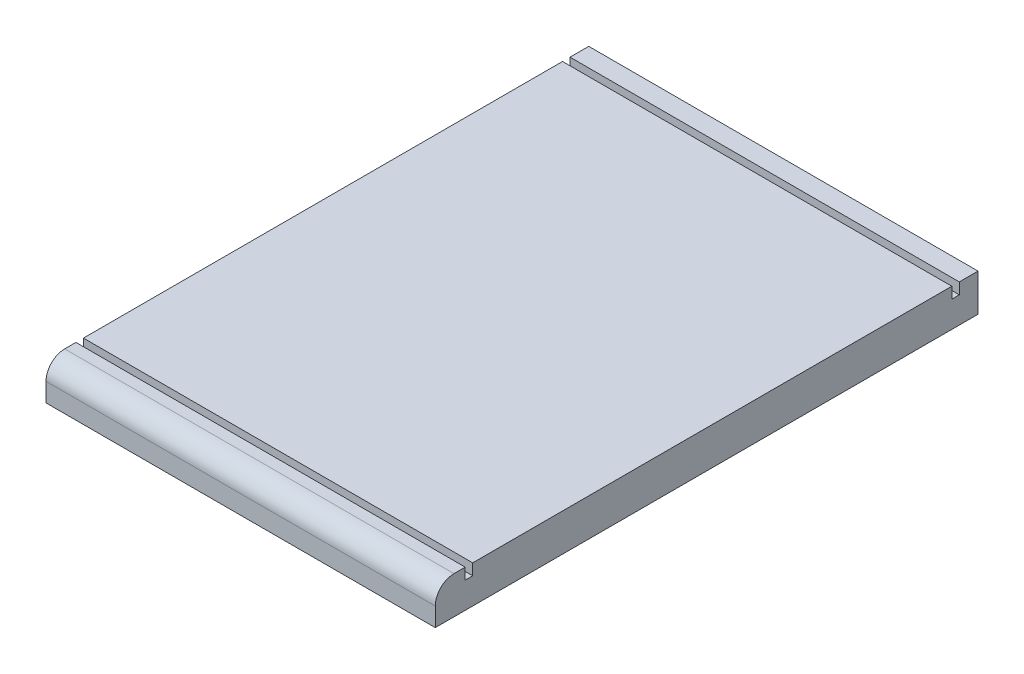
SolidWorks part; units mm, degrees
material "Mahogany"
ref_plane "Front Plane" through (0, 0, 0) normal (0, 0, 1) x (1, 0, 0)
ref_plane "Top Plane" through (0, 0, 0) normal (0, 1, 0) x (1, 0, 0)
ref_plane "Right Plane" through (0, 0, 0) normal (1, 0, 0) x (0, 0, -1)
sketch "Sketch1" plane through (0, 0, 0) normal (0, 1, 0) x (1, 0, 0)
  line L1 (-52, -72.5) -> (52, -72.5)
  line L2 (-52, -72.5) -> (-52, 72.5)
  line L3 (-52, 72.5) -> (52, 72.5)
  line L4 (52, -72.5) -> (52, 72.5)
  line L5 (-52, -72.5) -> (52, 72.5) construction
  line L6 (-52, 72.5) -> (52, -72.5) construction
  point P0 (0, 0)
  dimension "D1" = 104
  dimension "D2" = 145
extrude "Boss-Extrude1" add sketch "Sketch1" along normal blind 10
sketch "Sketch2" plane through (0, 10, 0) normal (0, 1, 0) x (1, 0, 0)
  line L0 (-52, 72.5) -> (-52, -72.5) construction
  line L1 (-52, 67.5) -> (52, 67.5)
  line L2 (-52, 67.5) -> (-52, 65.5)
  line L3 (-52, 65.5) -> (52, 65.5)
  line L4 (52, 67.5) -> (52, 65.5)
  line L5 (52, -72.5) -> (52, 72.5) construction
  line L6 (52, 72.5) -> (-52, 72.5) construction
  line L7 (-52, -62.5) -> (52, -62.5)
  line L8 (-52, -62.5) -> (-52, -64.5)
  line L9 (-52, -64.5) -> (52, -64.5)
  line L10 (52, -62.5) -> (52, -64.5)
  dimension "D1" = 2
  dimension "D2" = 2
  dimension "D3" = 5
  dimension "D4" = 130
extrude "Cut-Extrude1" cut sketch "Sketch2" against normal blind 3
fillet "Fillet2" radius 5 1 edges at (0, 10, 72.5)
